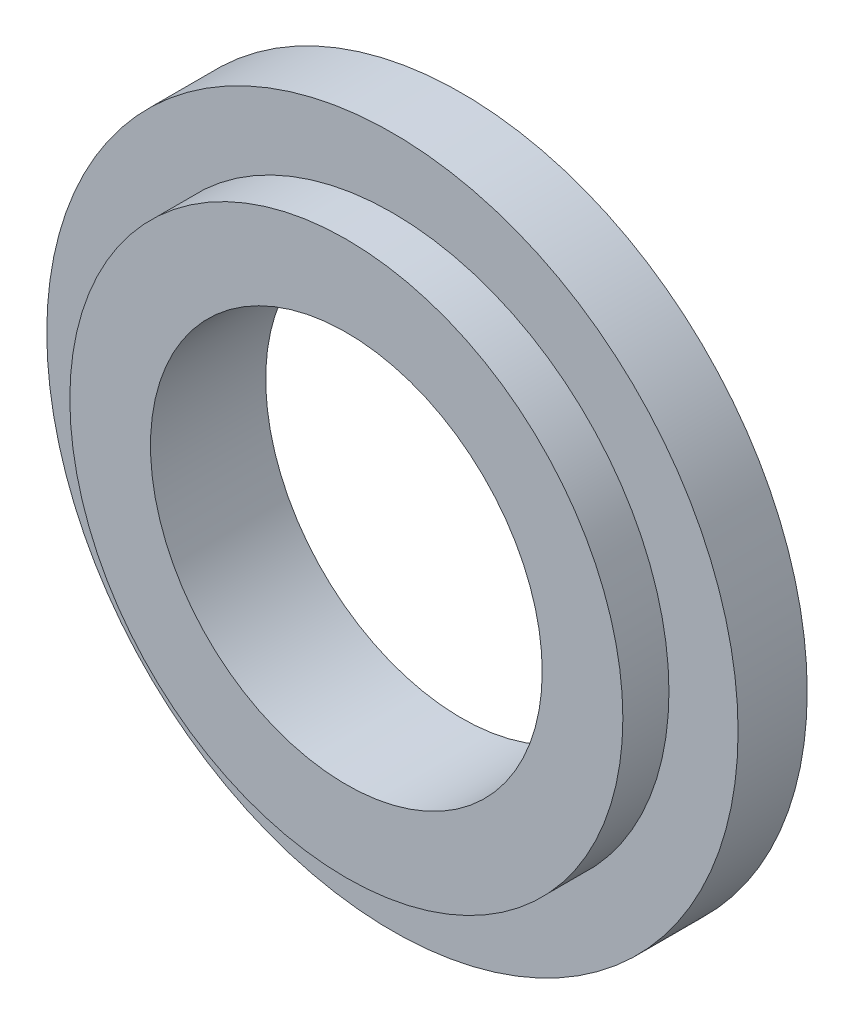
SolidWorks part; units mm, degrees
material "1023 Carbon Steel Sheet (SS)"
ref_plane "Front" through (0, 0, 0) normal (0, 0, 1) x (1, 0, 0)
ref_plane "Top" through (0, 0, 0) normal (0, 1, 0) x (1, 0, 0)
ref_plane "Right" through (0, 0, 0) normal (1, 0, 0) x (0, 0, -1)
sketch "Sketch1" plane through (0, 0, 0) normal (0, 0, 1) x (1, 0, 0)
  circle A0 centre (0, 0) radius 15
  circle A1 centre (0, 0) radius 8.5
  dimension "D1" = 30
  dimension "D2" = 17
extrude "Boss-Extrude1" add sketch "Sketch1" along normal blind 3
sketch "Sketch2" plane through (0, 0, 3) normal (0, 0, 1) x (1, 0, 0)
  circle A0 centre (0, 0) radius 8.5
  circle A1 centre (0, 0) radius 8.5 construction
  circle A2 centre (0, 0) radius 12
  dimension "D1" = 24
extrude "Boss-Extrude2" add sketch "Sketch2" along normal blind 2
